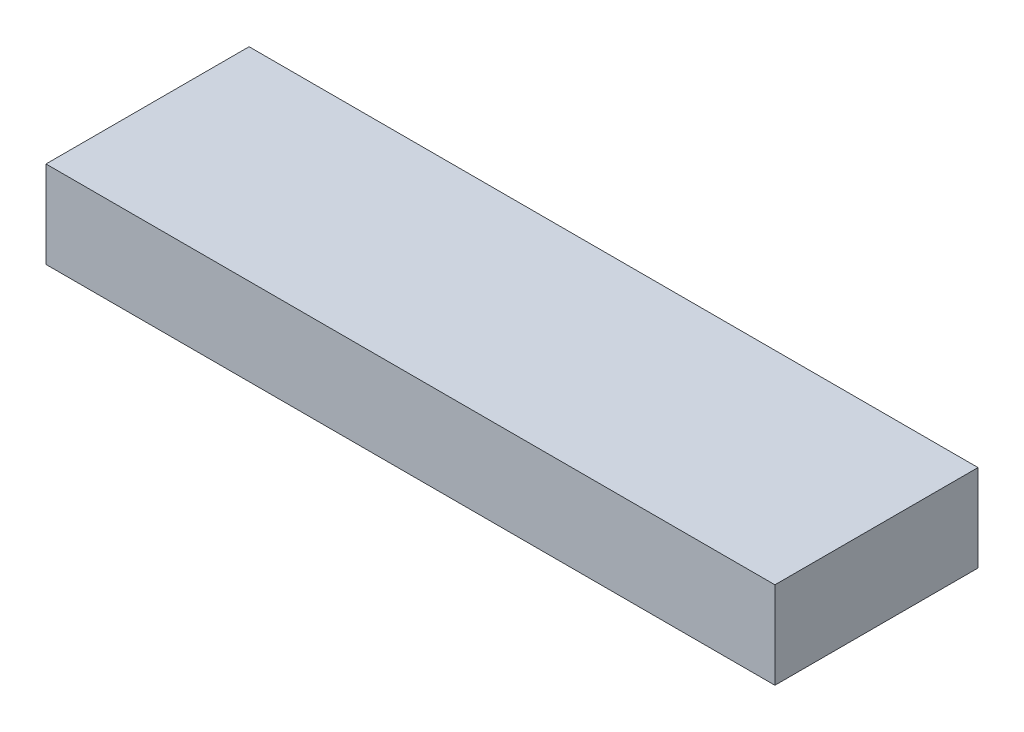
SolidWorks part; units mm, degrees
material "Pine"
ref_plane "Front Plane" through (0, 0, 0) normal (0, 0, 1) x (1, 0, 0)
ref_plane "Top Plane" through (0, 0, 0) normal (0, 1, 0) x (1, 0, 0)
ref_plane "Right Plane" through (0, 0, 0) normal (1, 0, 0) x (0, 0, -1)
sketch "Sketch1" plane through (0, 0, 0) normal (0, 1, 0) x (1, 0, 0)
  line L1 (0, 0) -> (319.0875, 0)
  line L2 (0, 0) -> (0, 88.9)
  line L3 (0, 88.9) -> (319.0875, 88.9)
  line L4 (319.0875, 0) -> (319.0875, 88.9)
  dimension "D1" = 88.9
  dimension "D2" = 319.0875
extrude "Boss-Extrude1" add sketch "Sketch1" along normal blind 38.1
